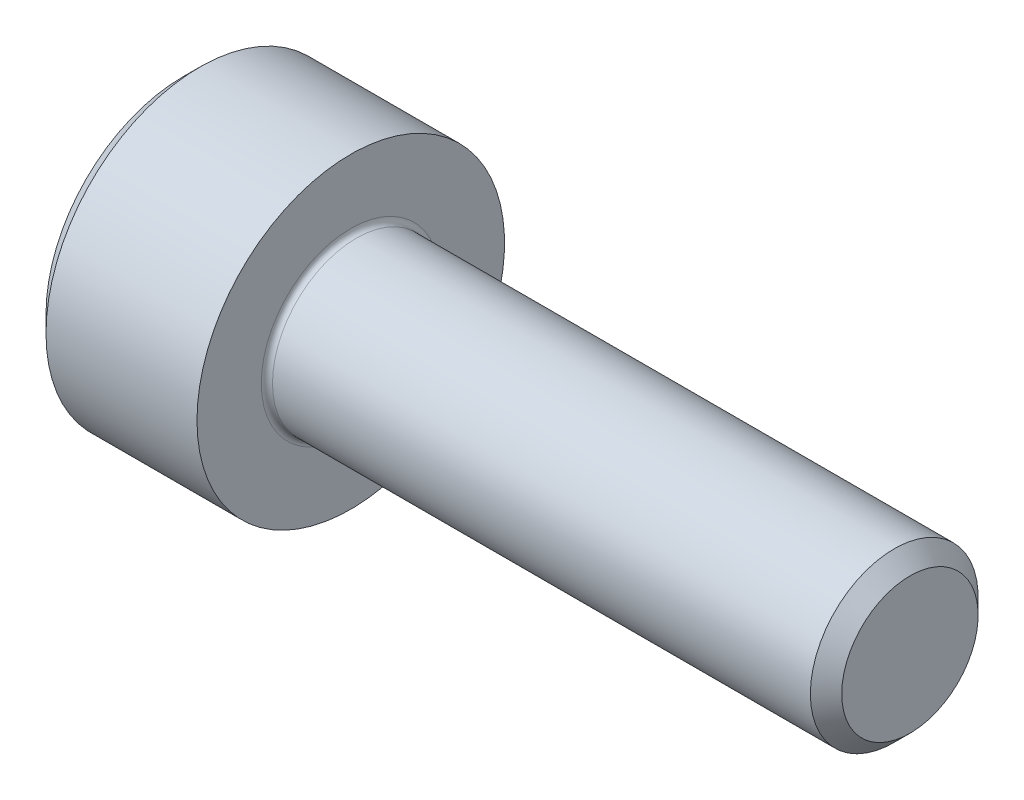
SolidWorks part; units mm, degrees
revolve "Base-Revolve" add sketch "BodySke"
sketch "BodySke" plane through (0, 0, 0) normal (0, 0, 1) x (1, 0, 0)
  line L0 (0, 0) -> (0, 2.45)
  line L1 (0.3, 2.75) -> (3, 2.75)
  line L2 (3, 2.75) -> (3, 1.5)
  line L3 (3, 1.5) -> (12.7195, 1.5)
  line L4 (13, 1.2195) -> (13, 0)
  line L5 (13, 0) -> (0, 0)
  line L6 (-31.75, 0) -> (127, 0) construction
  line L7 (0, 2.45) -> (0.3, 2.75)
  line L8 (13, 1.2195) -> (12.7195, 1.5)
  line L9 (0, -2.45) -> (0.3, -2.75) construction
  line L10 (13, -1.2195) -> (12.7195, -1.5) construction
  line L11 (3.5, 9.525) -> (3.5, 3.175) construction
  line L12 (3, 9.525) -> (3, 3.175) construction
  line L13 (-37, 9.525) -> (-37, 3.175) construction
  dimension "Diameter" = 3
  dimension "Head_ht" = 3
  dimension "Length" = 10
  dimension "Body_ch_ang" = 45
  dimension "Head_dia" = 5.5
  dimension "Head_ch_ang" = 45
  dimension "Minor_dia" = 2.439
  dimension "Advance" = 0.5
  dimension "Thread_nom" = 10
  dimension "Thread_length" = 50
  dimension "Head_ch_ht" = 0.3
cosmetic thread "ThreadCosmetic" [suppressed]
fillet "Fillet1" radius 0.1 1 edges at (3, 0, 1.5)
material "Plain Carbon Steel"
ref_plane "Plane1" through (0, 0, 0) normal (0, 0, 1) x (1, 0, 0)
ref_plane "Plane2" through (0, 0, 0) normal (0, 1, 0) x (1, 0, 0)
ref_plane "Plane3" through (0, 0, 0) normal (1, 0, 0) x (0, 0, -1)
sketch "Sketch2" plane through (0, 0, 0) normal (0, 0, 1) x (1, 0, 0)
  line L0 (0, 1.28) -> (1.3, 1.28)
  line L1 (1.3, 1.28) -> (2.039, 0)
  line L2 (-31.75, 0) -> (127, 0) construction
  line L3 (2.039, 0) -> (0, 0)
  line L4 (0, 0) -> (0, 1.28)
  line L5 (0, 2.45) -> (0, -2.45) construction
  line L6 (0, 0) -> (47.625, 0) construction
  line L7 (3, -2.75) -> (3, 2.75) construction
  dimension "D1" = 1.28
  dimension "D2" = 60
revolve "Hex-PreBroach" cut sketch "Sketch2" angle 360 about L6
sketch "Sketch3" plane through (0, 0, 0) normal (-1, 0, 0) x (0, 0.5, 0.866)
  line L0 (0.739, 1.28) -> (-0.739, 1.28)
  line L1 (-0.739, 1.28) -> (-1.478, 0)
  line L2 (0.739, 1.28) -> (1.478, 0)
  line L3 (0.739, -1.28) -> (1.478, 0)
  line L4 (0.739, -1.28) -> (-0.739, -1.28)
  line L5 (-0.739, -1.28) -> (-1.478, 0)
  dimension "D1" = 1.28
  dimension "D2" = 1.28
  dimension "Hex_size" = 2.56
extrude "Hex" cut sketch "Sketch3" against normal blind 1.3
sketch "Sketch4" plane through (0, 0, 0) normal (-1, 0, 0) x (0, 0, 1)
  line L0 (0, 0) -> (1.4605, 0)
  line L1 (0, 0) -> (6.1484, 3.5498) construction
  line L2 (0, 0) -> (0.7302, 1.2648)
  line L3 (1.2009, 0.3267) -> (1.3933, 0.4378)
  line L4 (0.8834, 0.8767) -> (1.0758, 0.9877)
  arc A0 (1.2009, 0.3267) -> (0.8834, 0.8767) centre (0, 0) ccw
  arc A1 (1.4605, 0) -> (1.3933, 0.4378) centre (0, 0) ccw
  arc A2 (0.7302, 1.2648) -> (1.0758, 0.9877) centre (0, 0) cw
  dimension "D1" = 30
  dimension "D2" = 60
  dimension "Spline_p_dim" = 0.635
  dimension "D3" = 0.3175
extrude "Spline" [suppressed] cut sketch "Sketch4" against normal blind 1.3
pattern_circular "CirPattern1" [suppressed] count 6 every 60
sketch "Sketch5" plane through (0, 0, 0) normal (0, 0, 1) x (1, 0, 0)
  line L0 (-31.75, 0) -> (127, 0) construction
  line L2 (0, 2.45) -> (0, -2.45) construction
  circle A0 centre (1.2, 0) radius 0.475
  dimension "Drilled_hole_dia" = 0.95
  dimension "Drilled_hole_loc" = 1.2
extrude "Hole" [suppressed] cut sketch "Sketch5" against normal through all and the other way through all
pattern_circular "Drilled-4" [suppressed] count 2 every 60
pattern_circular "Drilled-6" [suppressed] count 3 every 60
sketch "ThdSchSke" plane through (0, 0, 0) normal (0, 0, 1) x (1, 0, 0)
  line L0 (3.5, -1.2195) -> (3.3036, -1.5)
  line L1 (3.5, -1.2195) -> (3.6964, -1.5)
  line L2 (3.6964, -1.5) -> (3.6964, -1.875)
  line L3 (-3.175, 0) -> (5.1513, 0) construction
  line L5 (3.6964, -1.875) -> (3.3036, -1.875)
  line L6 (3.3036, -1.875) -> (3.3036, -1.5)
  line L7 (0, 2.45) -> (0, -2.45) construction
  dimension "Thread_minor" = 2.439
  dimension "Diameter" = 3
  dimension "Start" = 3.5
revolve "ThreadSchematic" [suppressed] cut sketch "ThdSchSke" angle 360 about L3
pattern_linear "ThdSchPat" [suppressed]
equation "\"D2@Sketch3\" = \"Hex_size@Sketch3\" / 2"
equation "\"D1@Sketch3\" = \"Hex_size@Sketch3\" / 2"
equation "\"D1@Sketch2\" = \"Hex_size@Sketch3\" / 2"
equation "\"D3@Sketch4\" = \"Spline_p_dim@Sketch4\" / 2"
equation "\"Thread_minor@ThreadCosmetic\"  =  \"Minor_dia@BodySke\""
equation "\"D2@CirPattern1\" = 360 / \"Num_teeth@CirPattern1\""
equation "\"Wall_thickness@Sketch2\" = \"Head_ht@BodySke\" - \"Key_eng@Hex\""
equation "\"Thread_length@ThreadCosmetic\" = ((sgn( (\"Length@BodySke\" - \"Advance@BodySke\" ) - \"Thread_nom@BodySke\" )-1)*( (\"Length@BodySke\" - \"Advance@BodySke\" ) - \"Thread_nom@BodySke\" ))/-2+ \"Thread_nom@BodySke\""
equation "\"Thread_minor@ThdSchSke\" = \"Minor_dia@BodySke\""
equation "\"Diameter@ThdSchSke\" = \"Diameter@BodySke\""
equation "\"Overcut@ThdSchSke\" = \"Diameter@BodySke\" * 1.25"
equation "\"Start@ThdSchSke\" = \"Head_ht@BodySke\" + \"Length@BodySke\" - \"Thread_length@ThreadCosmetic\"  '---Non-countersunk---"
equation "\"Num_threads@ThdSchPat\" = int( \"Thread_length@ThreadCosmetic\" / \"Advance@BodySke\" + 0.999 )  + 1"
equation "\"Advance@ThdSchPat\" = \"Thread_length@ThreadCosmetic\" /  (\"Num_threads@ThdSchPat\" - 1) 'relax it"
equation "\"Num_threads@ThdSchPat\" = \"Num_threads@ThdSchPat\" - sgn( \"Num_threads@ThdSchPat\" - 1) '---chamfered tips only---"
